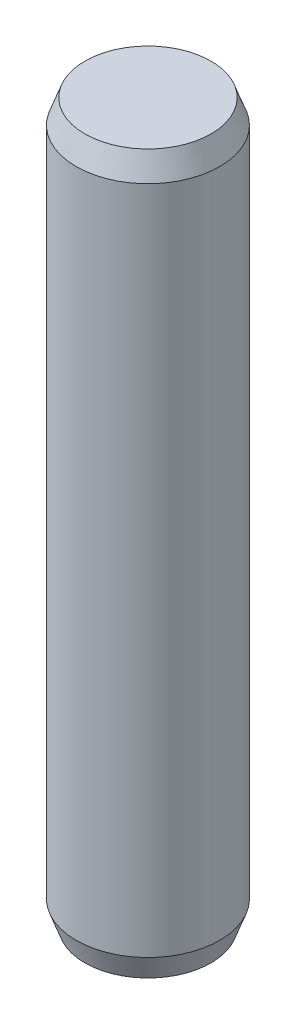
SolidWorks part; units mm, degrees
material "1023 Carbon Steel Sheet (SS)"
ref_plane "Front Plane" through (0, 0, 0) normal (0, 0, 1) x (1, 0, 0)
ref_plane "Top Plane" through (0, 0, 0) normal (0, 1, 0) x (1, 0, 0)
ref_plane "Right Plane" through (0, 0, 0) normal (1, 0, 0) x (0, 0, -1)
sketch "Sketch1" plane through (0, 0, 0) normal (0, 1, 0) x (1, 0, 0)
  circle A0 centre (0, 0) radius 3
  dimension "D1" = 6
extrude "Boss-Extrude1" add sketch "Sketch1" along normal blind 30
chamfer "Chamfer1" distance 1 angle 20 1 edges at (0, 30, 3)
chamfer "Chamfer2" distance 1 angle 20 1 edges at (0, 0, 3)
